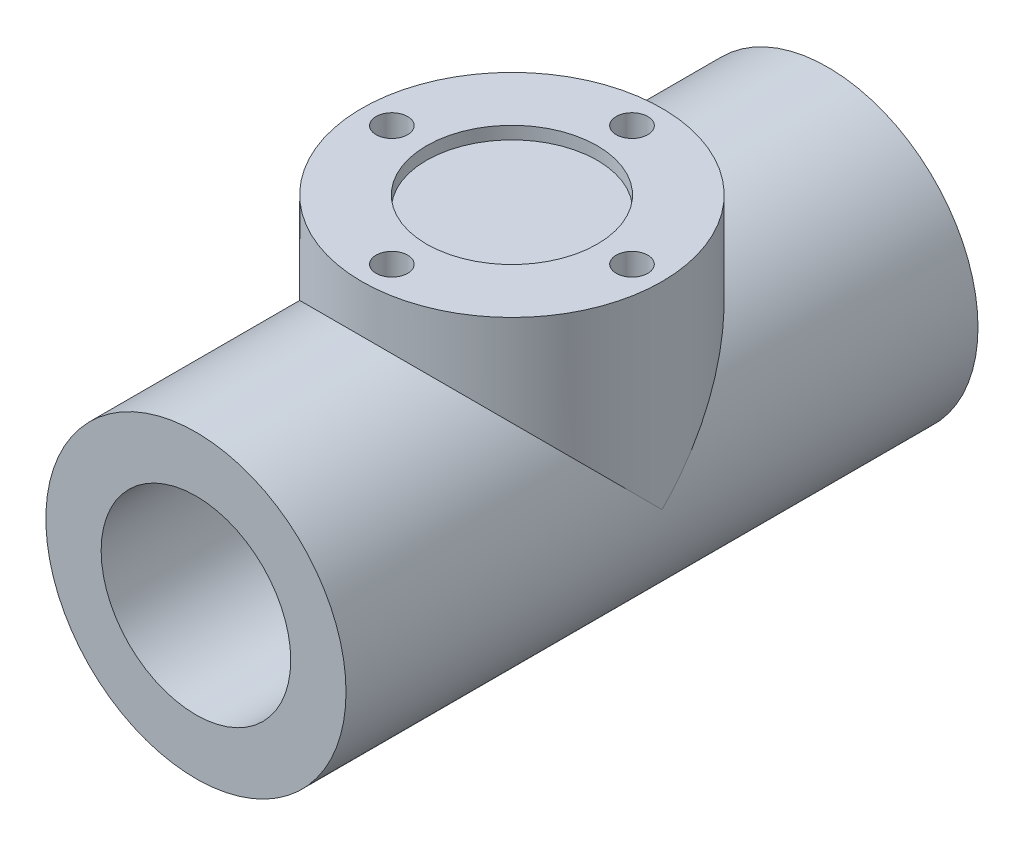
SolidWorks part; units mm, degrees
material "Ti-6Al-4VSolution treated and aged (SS)"
ref_plane "Front Plane" through (0, 0, 0) normal (0, 0, 1) x (1, 0, 0)
ref_plane "Top Plane" through (0, 0, 0) normal (0, 1, 0) x (1, 0, 0)
ref_plane "Right Plane" through (0, 0, 0) normal (1, 0, 0) x (0, 0, -1)
sketch "Sketch1" plane through (0, 0, 0) normal (0, 0, 1) x (1, 0, 0)
  circle A0 centre (0, 0) radius 47.5
  dimension "D1" = 95
extrude "Boss-Extrude1" add sketch "Sketch1" along normal mid plane 200
sketch "Sketch2" plane through (0, 0, 0) normal (0, 1, 0) x (1, 0, 0)
  circle A0 centre (0, 0) radius 47.5
  dimension "D1" = 95
extrude "Boss-Extrude2" add sketch "Sketch2" along normal blind 62.5
sketch "Sketch3" plane through (0, 62.5, 0) normal (0, 1, 0) x (1, 0, 0)
  circle A0 centre (0, 0) radius 27
  dimension "D1" = 54
extrude "Cut-Extrude1" cut sketch "Sketch3" against normal blind 4
sketch "Sketch4" plane through (0, 62.5, 0) normal (0, 1, 0) x (1, 0, 0)
  line L0 (0, 117.906) -> (0, -153.0348) construction
  line L1 (-89.8776, 0) -> (179.1946, 0) construction
  circle A0 centre (0, 0) radius 38 construction
  dimension "D1" = 76
hole_wizard "Hole1" positions "3DSketch1" profile "Sketch5" legacy
sketch3d "3DSketch1"
  line L0 (-89.8776, 62.5, 0) -> (179.1946, 62.5, 0) construction
  line L1 (0, 62.5, -117.906) -> (0, 62.5, 153.0348) construction
  circle A0 centre (0, 62.5, 0) radius 38 construction
  point P0 (38, 62.5, 0)
  point P6 (0, 100.5, 0)
  point P7 (0, 62.5, -38)
  point P11 (-38, 62.5, 0)
  point P13 (0, 62.5, 38)
sketch "Sketch5" plane through (38, 62.5, 0) normal (1, 0, 0) x (0, 0, 1)
  line L0 (0, 0) -> (0, 20)
  line L1 (0, 20) -> (5, 20)
  line L2 (5, 20) -> (5, 0)
  line L3 (5, 0) -> (0, 0)
  line L4 (0, 110) -> (0, -10) construction
  dimension "Diameter" = 10
  dimension "Depth" = 20
sketch "Sketch6" plane through (0, 0, -100) normal (0, 0, -1) x (-1, 0, 0)
  circle A0 centre (0, 0) radius 30
  dimension "D1" = 60
extrude "Cut-Extrude2" cut sketch "Sketch6" against normal up to surface (200 mm away) up to face at (47.5, 0, 100)
